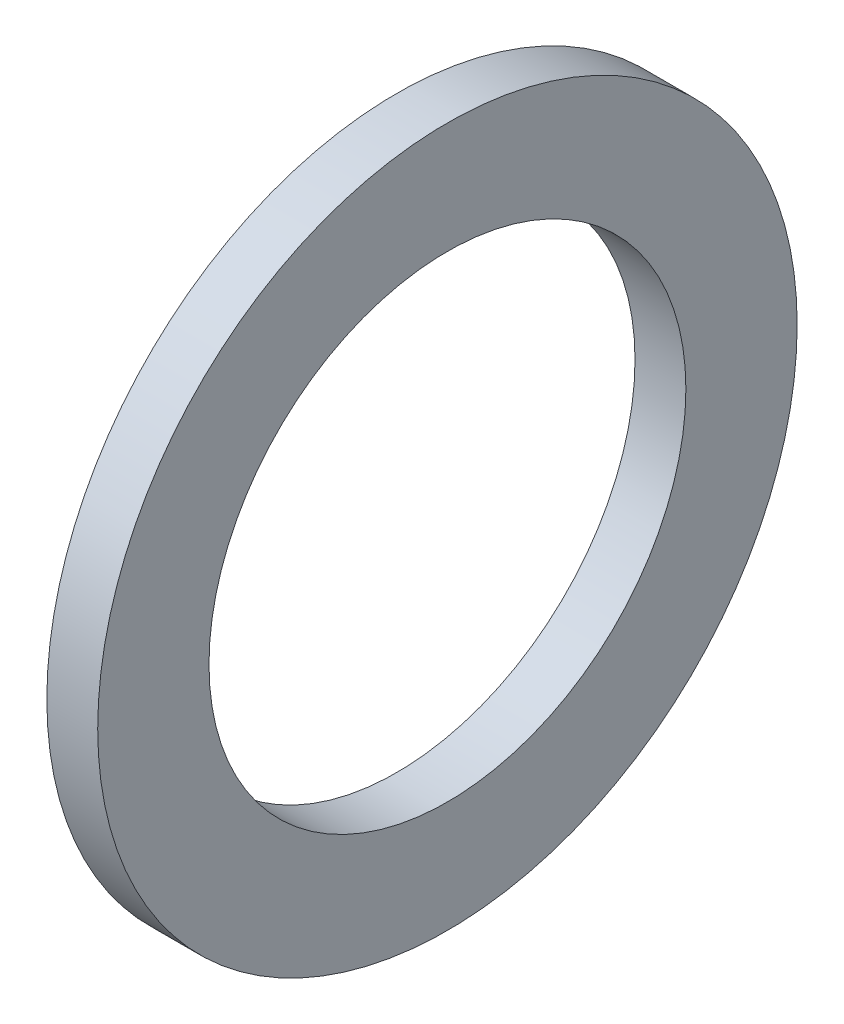
SolidWorks part; units mm, degrees
ref_plane "Front Plane" through (0, 0, 0) normal (0, 0, 1) x (1, 0, 0)
ref_plane "Top Plane" through (0, 0, 0) normal (0, 1, 0) x (1, 0, 0)
ref_plane "Right Plane" through (0, 0, 0) normal (1, 0, 0) x (0, 0, -1)
sketch "Sketch1" plane through (0, 0, 0) normal (1, 0, 0) x (0, 0, -1)
  circle A0 centre (0, 0) radius 7.5
  circle A1 centre (0, 0) radius 11
  dimension "D1" = 15
  dimension "D2" = 22
extrude "Boss-Extrude1" add sketch "Sketch1" along normal blind 1.6
